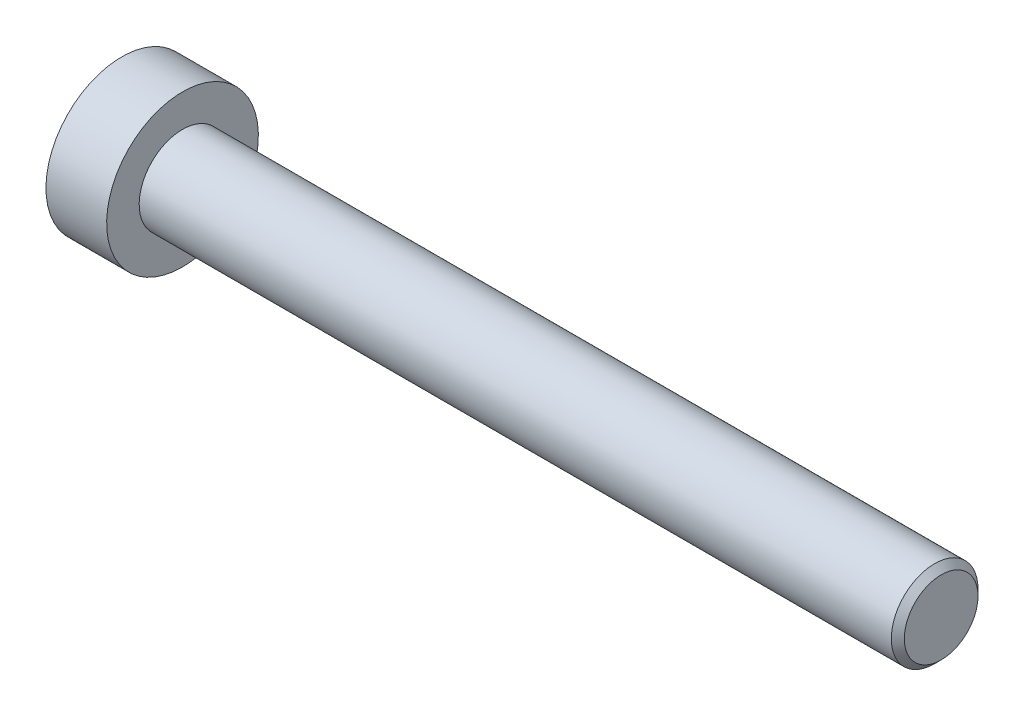
SolidWorks part; units mm, degrees
material "Plain Carbon Steel"
ref_plane "Front Plane" through (0, 0, 0) normal (0, 0, 1) x (1, 0, 0)
ref_plane "Top Plane" through (0, 0, 0) normal (0, 1, 0) x (1, 0, 0)
ref_plane "Right Plane" through (0, 0, 0) normal (1, 0, 0) x (0, 0, -1)
sketch "Sketch2" plane through (0, 0, 0) normal (1, 0, 0) x (0, 0, -1)
  circle A0 centre (0, 0) radius 2
  dimension "D1" = 4
extrude "Boss-Extrude1" add sketch "Sketch2" against normal blind 35
chamfer "Chamfer1" distance 0.3 angle 45 1 edges at (0, 0, -2)
sketch "Sketch6" plane through (0, 0, 0) normal (0, 0, 1) x (1, 0, 0)
  line L0 (-37.8, 0) -> (-37.8, 3.5)
  line L1 (-37.8, 0) -> (-35, 0)
  line L2 (-37.8, 3.5) -> (-35, 3.5)
  line L6 (-35, 3.5) -> (-35, 0)
  line L8 (-35, 0) -> (-14.6471, 0) construction
  line L10 (-35, 2) -> (-35, -2) construction
  dimension "D1" = 2.8
  dimension "D2" = 7
revolve "Revolve1" add sketch "Sketch6" angle 360 about L8
sketch "Sketch7" plane through (-37.8, 0, 0) normal (-1, 0, 0) x (0, 0, 1)
  line L1 (0, 1.4434) -> (-1.25, 0.7217)
  line L2 (-1.25, 0.7217) -> (-1.25, -0.7217)
  line L3 (-1.25, -0.7217) -> (0, -1.4434)
  line L4 (0, -1.4434) -> (1.25, -0.7217)
  line L5 (1.25, -0.7217) -> (1.25, 0.7217)
  line L6 (1.25, 0.7217) -> (0, 1.4434)
  circle A0 centre (0, 0) radius 1.25 construction
  dimension "D1" = 2.5
extrude "Cut-Extrude1" cut sketch "Sketch7" against normal blind 1.6
sketch "Sketch8" plane through (-37.8, 0, 0) normal (-1, 0, 0) x (0, 0, 1)
  circle A0 centre (0, 0) radius 1.4934
  dimension "D1" = 0.05
extrude "Cut-Extrude2" cut sketch "Sketch8" against normal blind 1 draft 45
